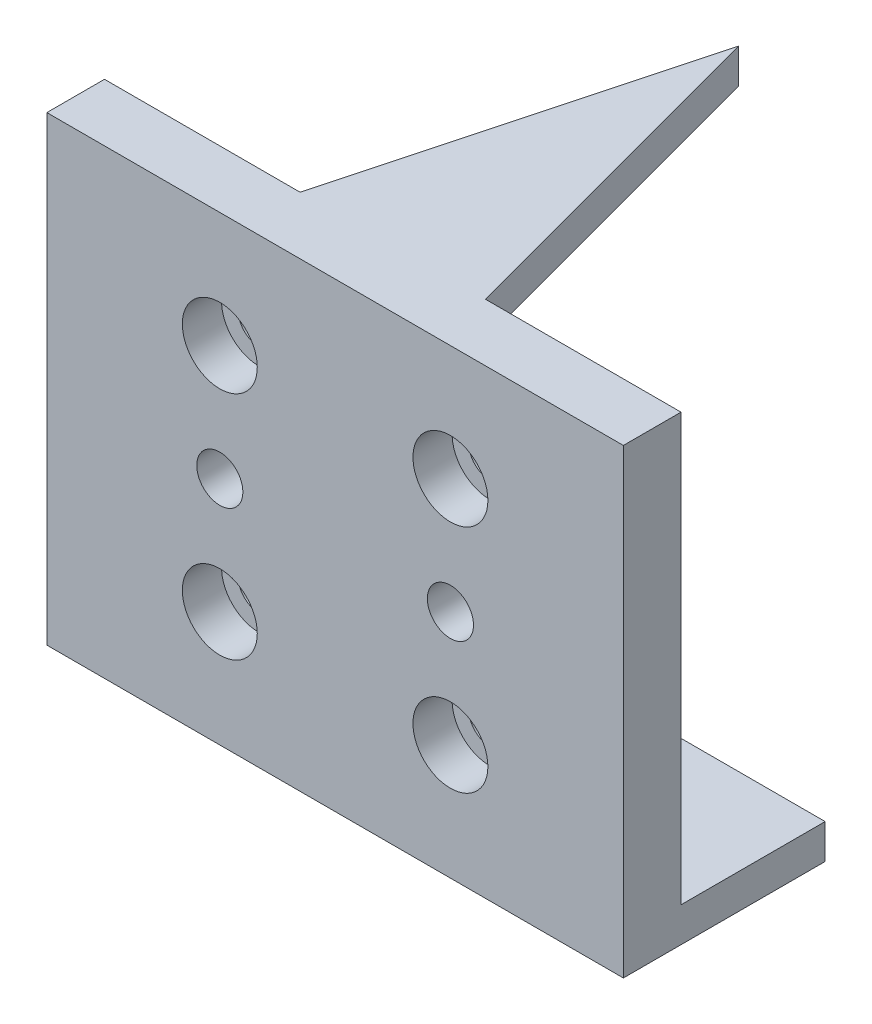
SolidWorks part; units mm, degrees
material "Allzweck-PBT"
ref_plane "Ebene vorne" through (0, 0, 0) normal (0, 0, 1) x (1, 0, 0)
ref_plane "Ebene oben" through (0, 0, 0) normal (0, 1, 0) x (1, 0, 0)
ref_plane "Ebene rechts" through (0, 0, 0) normal (1, 0, 0) x (0, 0, -1)
sketch "Skizze1" plane through (0, 0, 0) normal (0, 0, 1) x (1, 0, 0)
  line L1 (0, 0) -> (50, 0)
  line L2 (0, 0) -> (0, -40)
  line L3 (0, -40) -> (50, -40)
  line L4 (50, 0) -> (50, -40)
  dimension "D1" = 50
  dimension "D2" = 40
extrude "Aufsatz-Linear austragen1" add sketch "Skizze1" along normal blind 5
sketch "Skizze2" plane through (0, 0, 0) normal (0, 1, 0) x (1, 0, 0)
  line L0 (25, 0) -> (25, 30) construction
  line L1 (50, 0) -> (0, 0) construction
  line L2 (25, 30) -> (16.9615, 0)
  line L3 (25, 30) -> (33.0385, 0)
  line L4 (33.0385, 0) -> (16.9615, 0)
  dimension "D1" = 30
  dimension "D2" = 105
  dimension "D3" = 105
extrude "Aufsatz-Linear austragen2" add sketch "Skizze2" against normal blind 3
hole_wizard "Stirnsenkung für M3 Zylinderschraube mit Innensechskant1" positions "Skizze4" profile "Skizze5" counterbore size "M3" standard "DIN" end condition up to next
sketch "Skizze4" plane through (0, 0, 5) normal (0, 0, 1) x (1, 0, 0)
  line L1 (15, -10) -> (35, -10) construction
  line L2 (15, -10) -> (15, -30) construction
  line L3 (15, -30) -> (35, -30) construction
  line L4 (35, -10) -> (35, -30) construction
  line L5 (0, 0) -> (0, -40) construction
  line L6 (50, 0) -> (0, 0) construction
  point P0 (15, -10)
  point P2 (35, -10)
  point P4 (35, -30)
  point P6 (15, -30)
  dimension "D1" = 20
  dimension "D2" = 20
  dimension "D3" = 20
  dimension "D4" = 20
  dimension "D5" = 15
  dimension "D6" = 10
sketch "Skizze5" plane through (15, -10, 5) normal (1, 0, 0) x (0, -1, 0)
  line L0 (0, 0) -> (0, 5)
  line L1 (0, 5) -> (1.8, 5)
  line L3 (1.8, 5) -> (1.8, 3.4)
  line L4 (1.8, 3.4) -> (3.25, 3.4)
  line L5 (3.25, 3.4) -> (3.25, 0)
  line L7 (3.25, 0) -> (0, 0)
  line L11 (0, -6.35) -> (0, 107.95) construction
  dimension "Bohrerdurchmesser" = 3.6
  dimension "Bohrungstiefe" = 5
  dimension "Senkdurchmesser2" = 6.5
  dimension "Senktiefe2" = 3.4
sketch "Skizze6" plane through (0, 0, 5) normal (0, 0, 1) x (1, 0, 0)
  line L0 (0, -20) -> (50, -20) construction
  line L1 (0, 0) -> (0, -40) construction
  line L2 (50, -40) -> (50, 0) construction
  circle A0 centre (15, -20) radius 2
  circle A1 centre (35, -20) radius 2
  dimension "D3" = 4
  dimension "D4" = 4
  dimension "D1" = 15
  dimension "D2" = 15
extrude "Schnitt-Linear austragen1" cut sketch "Skizze6" against normal through all
sketch "Skizze7" plane through (0, 0, 0) normal (0, 0, -1) x (-1, 0, 0)
  line L0 (0, 0) -> (0, -40) construction
  line L1 (-50, -40) -> (0, -40)
  line L2 (-50, -40) -> (-50, -37)
  line L3 (-50, -37) -> (0, -37)
  line L4 (0, -40) -> (0, -37)
  dimension "D1" = 3
extrude "Aufsatz-Linear austragen3" add sketch "Skizze7" along normal blind 12.5
